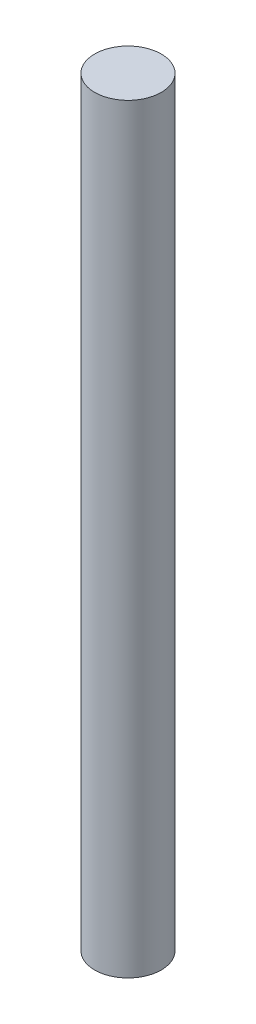
SolidWorks part; units mm, degrees
ref_plane "Front Plane" through (0, 0, 0) normal (0, 0, 1) x (1, 0, 0)
ref_plane "Top Plane" through (0, 0, 0) normal (0, 1, 0) x (1, 0, 0)
ref_plane "Right Plane" through (0, 0, 0) normal (1, 0, 0) x (0, 0, -1)
sketch "Sketch1" plane through (0, 0, 0) normal (0, 1, 0) x (1, 0, 0)
  circle A0 centre (0, 0) radius 12.7
  dimension "D1" = 25.4
extrude "Boss-Extrude1" add sketch "Sketch1" along normal blind 290
sketch "Sketch2" plane through (0, 290, 0) normal (0, 1, 0) x (1, 0, 0)
  point P0 (0, 0)
sketch "Sketch3" plane through (0, 0, 0) normal (0, -1, 0) x (1, 0, 0)
  point P0 (0, 0)
